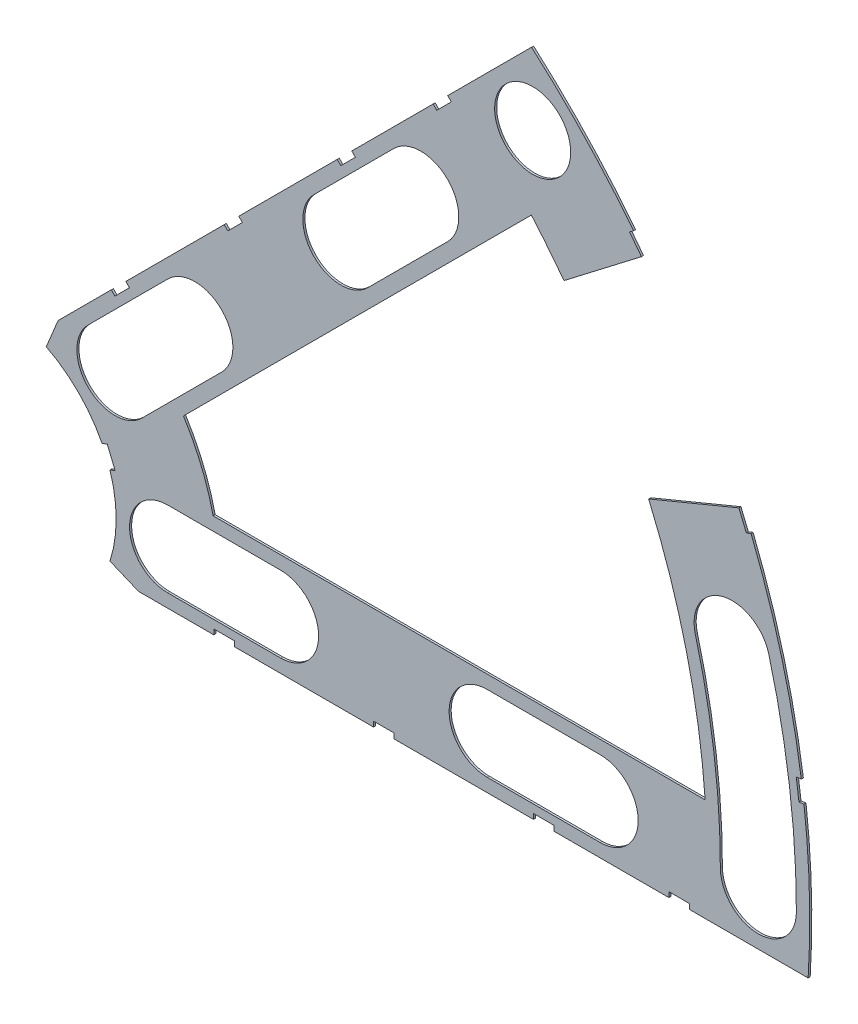
SolidWorks part; units mm, degrees
material "PTFE (general)"
ref_plane "Front Plane" through (0, 0, 0) normal (0, 0, 1) x (1, 0, 0)
ref_plane "Top Plane" through (0, 0, 0) normal (0, 1, 0) x (1, 0, 0)
ref_plane "Right Plane" through (0, 0, 0) normal (1, 0, 0) x (0, 0, -1)
sketch "Sketch1" plane through (0, 0, 0) normal (0, 0, 1) x (1, 0, 0)
  line L0 (0, 0) -> (320.3893, 0) construction
  line L1 (0, 0) -> (155.5285, 155.5285) construction
  line L2 (67.2115, 76.1917) -> (8.6967, 17.6769)
  line L3 (8.6967, 17.6769) -> (7.229, 14.1336)
  line L4 (101.4014, -6.35) -> (18.6489, -6.35)
  line L5 (15.1056, -4.8823) -> (18.6489, -6.35)
  line L6 (88.6729, 6.35) -> (27.8605, 6.35)
  line L9 (67.1914, 58.2111) -> (24.1905, 15.2102)
  line L10 (0, 0) -> (40.4486, 97.6516) construction
  line L11 (0, 0) -> (123.4567, -51.1374) construction
  line L18 (8.6967, 17.6769) -> (13.294, 8.6183) construction
  line L19 (18.6489, -6.35) -> (15.4943, 3.3063) construction
  line L20 (27.8605, 6.35) -> (27.7442, 6.7059) construction
  line L21 (24.1905, 15.2102) -> (24.3599, 14.8764) construction
  arc A0 (7.229, 14.1336) -> (15.1056, -4.8823) centre (0, 0) cw
  arc A1 (67.2115, 76.1917) -> (101.4014, -6.35) centre (0, 0) cw
  arc A2 (24.1905, 15.2102) -> (27.8605, 6.35) centre (0, 0) cw
  arc A3 (67.1914, 58.2111) -> (88.6729, 6.35) centre (0, 0) cw
  arc A8 (13.294, 8.6183) -> (15.4943, 3.3063) centre (0, 0) cw construction
  arc A9 (24.3599, 14.8764) -> (27.7442, 6.7059) centre (0, 0) cw construction
  dimension "D1" = 45
  dimension "D3" = 6.35
  dimension "D4" = 15.875
  dimension "D7" = 22.5
  dimension "D8" = 101.6
  dimension "D11" = 12.7
  dimension "D12" = 12.7
  dimension "D2" = 6.35
  dimension "D5" = 67.5
  dimension "D9" = 1.27
  dimension "D10" = 1.27
  dimension "D6" = 12.7
extrude "Boss-Extrude1" add sketch "Sketch1" along normal blind 0.254
sketch "Sketch2" plane through (0, 0, 0.254) normal (0, 0, 1) x (1, 0, 0)
  line L0 (0, 0) -> (101.6, 0) construction
  line L1 (0, 0) -> (71.842, 71.842) construction
  line L3 (0, 0) -> (22.225, 0) construction
  line L4 (0, 0) -> (15.7154, 15.7154) construction
  line L5 (0, 0) -> (95.25, 0) construction
  line L6 (0, 0) -> (92.0044, 24.6525) construction
  arc A0 (101.4014, -6.35) -> (67.2115, 76.1917) centre (0, 0) ccw construction
  circle A1 centre (22.225, 0) radius 4.699
  arc A2 (15.1056, -4.8823) -> (7.229, 14.1336) centre (0, 0) ccw construction
  circle A3 centre (36.195, 0) radius 4.699
  circle A4 centre (61.722, 0) radius 4.699
  circle A5 centre (75.692, 0) radius 4.699
  circle A6 centre (95.25, 0) radius 4.699
  circle A7 centre (15.7154, 15.7154) radius 4.699
  circle A8 centre (25.5937, 25.5937) radius 4.699
  circle A9 centre (43.644, 43.644) radius 4.699
  circle A10 centre (53.5223, 53.5223) radius 4.699
  circle A11 centre (92.0044, 24.6525) radius 4.699
  circle A12 centre (82.4889, 47.625) radius 4.699
  circle A13 centre (67.3519, 67.3519) radius 4.699
  dimension "D3" = 9.398
  dimension "D1" = 45
  dimension "D2" = 6.35
  dimension "D4" = 6.35
  dimension "D5" = 13.97
  dimension "D7" = 13.97
  dimension "D8" = 19.558
  dimension "D9" = 45
  dimension "D10" = 15
  dimension "D11" = 25.527
  dimension "D6" = 2
extrude "Cut-Extrude1" cut sketch "Sketch2" against normal through all
sketch "Sketch3" plane through (0, 0, 0.254) normal (0, 0, 1) x (1, 0, 0)
  line L0 (15.2664, 24.2467) -> (17.0625, 26.0427)
  line L1 (15.2664, 24.2467) -> (15.7154, 23.7977)
  line L2 (17.0625, 26.0427) -> (17.5115, 25.5937)
  line L3 (15.7154, 23.7977) -> (17.5115, 25.5937)
  line L4 (67.2115, 76.1917) -> (8.6967, 17.6769) construction
  line L5 (44.9911, 53.9713) -> (43.195, 52.1753)
  line L6 (44.9911, 53.9713) -> (45.4401, 53.5223)
  line L7 (43.195, 52.1753) -> (43.644, 51.7263)
  line L8 (45.4401, 53.5223) -> (43.644, 51.7263)
  line L9 (27.94, -6.35) -> (30.48, -6.35)
  line L10 (27.94, -6.35) -> (27.94, -5.715)
  line L11 (30.48, -6.35) -> (30.48, -5.715)
  line L12 (27.94, -5.715) -> (30.48, -5.715)
  line L13 (18.6489, -6.35) -> (101.4014, -6.35) construction
  line L14 (67.437, -6.35) -> (69.977, -6.35)
  line L15 (67.437, -6.35) -> (67.437, -5.715)
  line L16 (69.977, -6.35) -> (69.977, -5.715)
  line L17 (67.437, -5.715) -> (69.977, -5.715)
  line L18 (29.2307, 38.211) -> (31.0268, 40.007)
  line L19 (29.2307, 38.211) -> (29.6797, 37.762)
  line L20 (31.0268, 40.007) -> (31.4758, 39.558)
  line L21 (29.6797, 37.762) -> (31.4758, 39.558)
  line L22 (56.845, 65.8253) -> (55.049, 64.0292)
  line L23 (56.845, 65.8253) -> (57.294, 65.3763)
  line L24 (55.049, 64.0292) -> (55.498, 63.5802)
  line L25 (57.294, 65.3763) -> (55.498, 63.5802)
  line L26 (47.6885, -6.35) -> (50.2285, -6.35)
  line L27 (47.6885, -6.35) -> (47.6885, -5.715)
  line L28 (50.2285, -6.35) -> (50.2285, -5.715)
  line L29 (47.6885, -5.715) -> (50.2285, -5.715)
  line L30 (84.201, -6.35) -> (86.741, -6.35)
  line L31 (84.201, -6.35) -> (84.201, -5.715)
  line L32 (86.741, -6.35) -> (86.741, -5.715)
  line L33 (84.201, -5.715) -> (86.741, -5.715)
  line L34 (0, 0) -> (100.7308, 13.2615) construction
  line L35 (0, 0) -> (93.8662, 38.8806) construction
  line L36 (0, 0) -> (80.6047, 61.8502) construction
  line L37 (0, 0) -> (101.6, 0) construction
  line L38 (99.9355, 14.4377) -> (100.267, 11.9194)
  line L39 (99.9355, 14.4377) -> (101.1946, 14.6035)
  line L40 (100.267, 11.9194) -> (101.5261, 12.0852)
  line L41 (101.1946, 14.6035) -> (101.5261, 12.0852)
  line L42 (99.9355, 14.4377) -> (101.5261, 12.0852) construction
  line L43 (100.267, 11.9194) -> (101.1946, 14.6035) construction
  line L44 (93.7655, 37.4643) -> (94.9388, 37.9503)
  line L45 (93.7655, 37.4643) -> (92.7935, 39.811)
  line L46 (94.9388, 37.9503) -> (93.9668, 40.297)
  line L47 (92.7935, 39.811) -> (93.9668, 40.297)
  line L48 (93.7655, 37.4643) -> (93.9668, 40.297) construction
  line L49 (94.9388, 37.9503) -> (92.7935, 39.811) construction
  line L50 (79.3278, 62.4712) -> (80.874, 60.456)
  line L51 (79.3278, 62.4712) -> (80.3354, 63.2443)
  line L52 (80.874, 60.456) -> (81.8816, 61.2292)
  line L53 (80.3354, 63.2443) -> (81.8816, 61.2292)
  line L54 (79.3278, 62.4712) -> (81.8816, 61.2292) construction
  line L55 (80.874, 60.456) -> (80.3354, 63.2443) construction
  line L56 (13.5939, 7.0054) -> (14.5659, 4.6588)
  line L57 (13.5939, 7.0054) -> (14.7672, 7.4914)
  line L58 (14.5659, 4.6588) -> (15.7393, 5.1448)
  line L59 (14.7672, 7.4914) -> (15.7393, 5.1448)
  line L60 (13.5939, 7.0054) -> (15.7393, 5.1448) construction
  line L61 (14.5659, 4.6588) -> (14.7672, 7.4914) construction
  circle A0 centre (15.7154, 15.7154) radius 4.699 construction
  circle A1 centre (43.644, 43.644) radius 4.699 construction
  circle A2 centre (22.225, 0) radius 4.699 construction
  circle A3 centre (61.722, 0) radius 4.699 construction
  arc A4 (101.4014, -6.35) -> (67.2115, 76.1917) centre (0, 0) ccw construction
  arc A9 (15.1056, -4.8823) -> (7.229, 14.1336) centre (0, 0) ccw construction
  circle A10 centre (36.195, 0) radius 4.699 construction
  circle A11 centre (75.692, 0) radius 4.699 construction
  circle A12 centre (25.5937, 25.5937) radius 4.699 construction
  circle A13 centre (53.5223, 53.5223) radius 4.699 construction
  point P75 (14.6666, 6.0751)
  dimension "D2" = 5.715
  dimension "D3" = 2.54
  dimension "D6" = 5.715
  dimension "D8" = 0.635
  dimension "D9" = 5.715
  dimension "D12" = 5.715
  dimension "D4" = 7.5
  dimension "D5" = 22.5
  dimension "D7" = 37.5
  dimension "D10" = 90
  dimension "D11" = 1.27
  dimension "D14" = 0.635
  dimension "D15" = 90
  dimension "D18" = 0.635
  dimension "D19" = 90
  dimension "D22" = 0.635
  dimension "D20" = 1.27
  dimension "D17" = 0.635
  dimension "D13" = 11.4935
  dimension "D16" = 8.509
  dimension "D21" = 11.4935
  dimension "D23" = 8.509
extrude "Cut-Extrude2" cut sketch "Sketch3" against normal through all
sketch "Sketch5" plane through (0, 0, 0.254) normal (0, 0, 1) x (1, 0, 0)
  line L0 (0, 0) -> (85.7359, 65.7875) construction
  line L1 (0, 0) -> (99.6979, 41.2962) construction
  line L2 (69.977, -6.35) -> (84.201, -6.35) construction
  line L3 (93.7655, 37.4643) -> (94.3448, 37.7043) construction
  line L4 (70.2115, 52.4344) -> (82.303, 61.7126)
  line L5 (80.5153, 34.5877) -> (94.5962, 40.4202)
  line L6 (79.8253, 62.8529) -> (79.3278, 62.4712) construction
  arc A0 (80.5153, 34.5877) -> (70.2115, 52.4344) centre (0, 0) ccw
  arc A1 (94.5962, 40.4202) -> (82.303, 61.7126) centre (0, 0) ccw
  arc A2 (93.3728, 40.0509) -> (81.3715, 60.8378) centre (0, 0) ccw construction
  arc A3 (88.6729, 6.35) -> (67.1914, 58.2111) centre (0, 0) ccw construction
  dimension "D5" = 1.27
  dimension "D6" = 1.27
  dimension "D1" = 37.5
  dimension "D2" = 22.5
  dimension "D3" = 2.413
  dimension "D4" = 2.413
sketch "Sketch6" plane through (0, 0, 0.254) normal (0, 0, 1) x (1, 0, 0)
  line L0 (0, 0) -> (101.6, 0) construction
  line L1 (0, 0) -> (71.842, 71.842) construction
  line L2 (0, 0) -> (87.9882, 50.8) construction
  line L3 (0, 0) -> (98.1381, 26.296) construction
  line L4 (15.7154, 15.7154) -> (25.5937, 25.5937) construction
  line L5 (12.3928, 19.0381) -> (22.271, 28.9164)
  line L6 (19.0381, 12.3928) -> (28.9164, 22.271)
  line L7 (43.644, 43.644) -> (53.5223, 53.5223) construction
  line L8 (40.3213, 46.9667) -> (50.1996, 56.845)
  line L9 (46.9667, 40.3213) -> (56.845, 50.1996)
  line L10 (22.225, 0) -> (36.195, 0) construction
  line L11 (22.225, 4.699) -> (36.195, 4.699)
  line L12 (22.225, -4.699) -> (36.195, -4.699)
  line L13 (61.722, 0) -> (75.692, 0) construction
  line L14 (61.722, 4.699) -> (75.692, 4.699)
  line L15 (61.722, -4.699) -> (75.692, -4.699)
  arc A0 (79.8253, 62.8529) -> (67.2115, 76.1917) centre (0, 0) ccw construction
  arc A1 (12.3928, 19.0381) -> (19.0381, 12.3928) centre (15.7154, 15.7154) ccw
  arc A2 (28.9164, 22.271) -> (22.271, 28.9164) centre (25.5937, 25.5937) ccw
  arc A3 (40.3213, 46.9667) -> (46.9667, 40.3213) centre (43.644, 43.644) ccw
  arc A4 (56.845, 50.1996) -> (50.1996, 56.845) centre (53.5223, 53.5223) ccw
  arc A5 (101.4014, -6.35) -> (100.8887, 12.0013) centre (0, 0) ccw construction
  arc A6 (22.225, 4.699) -> (22.225, -4.699) centre (22.225, 0) ccw
  arc A7 (93.3728, 40.0509) -> (81.3715, 60.8378) centre (0, 0) ccw construction
  arc A8 (100.5572, 14.5196) -> (94.3448, 37.7043) centre (0, 0) ccw construction
  arc A9 (36.195, -4.699) -> (36.195, 4.699) centre (36.195, 0) ccw
  arc A10 (61.722, 4.699) -> (61.722, -4.699) centre (61.722, 0) ccw
  arc A11 (75.692, -4.699) -> (75.692, 4.699) centre (75.692, 0) ccw
  arc A12 (95.25, 0) -> (92.0044, 24.6525) centre (0, 0) ccw construction
  arc A13 (99.949, 0) -> (96.5433, 25.8687) centre (0, 0) ccw
  arc A14 (90.551, 0) -> (87.4655, 23.4363) centre (0, 0) ccw
  arc A15 (90.551, 0) -> (99.949, 0) centre (95.25, 0) ccw
  arc A16 (96.5433, 25.8687) -> (87.4655, 23.4363) centre (92.0044, 24.6525) ccw
  circle A17 centre (53.5223, 53.5223) radius 4.699 construction
  circle A18 centre (25.5937, 25.5937) radius 4.699 construction
  point P4 (20.6546, 20.6546)
  point P13 (48.5832, 48.5832)
  point P37 (29.21, 0)
  point P48 (68.707, 0)
  point P61 (94.4351, 12.4326)
  dimension "D3" = 9.398
  dimension "D1" = 45
  dimension "D4" = 9.398
  dimension "D5" = 9.398
extrude "Cut-Extrude4" cut sketch "Sketch6" against normal through all
extrude "Cut-Extrude5" cut sketch "Sketch5" against normal through all
equation "\"cSep\"= 1.005"
equation "\"D11@Sketch2\"=\"cSep\""
equation "\"cSep2\"= \"D8@Sketch2\""
equation "\"D13@Sketch3\"=\"cSep\"/2-.05"
equation "\"D16@Sketch3\"=\"cSep2\"/2-.05"
equation "\"D21@Sketch3\"=\"cSep\"/2-.05"
equation "\"D23@Sketch3\"=\"cSep2\"/2-.05"
